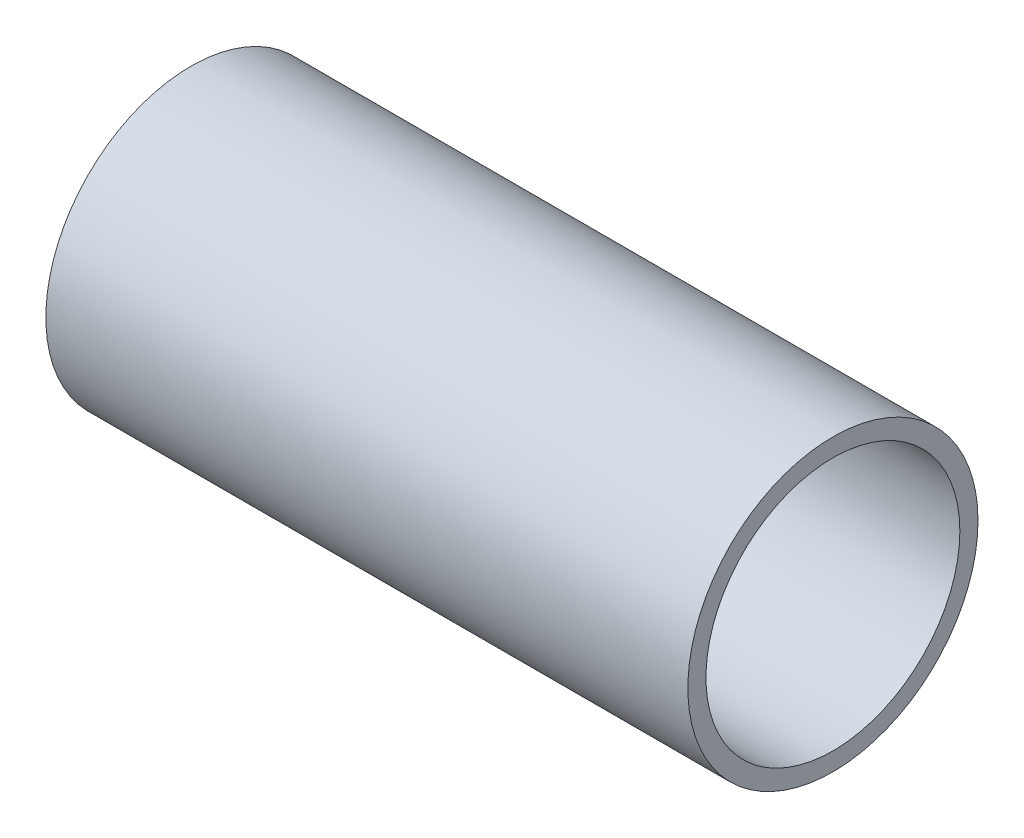
SolidWorks part; units mm, degrees
material "Bronce de aluminio"
ref_plane "Alzado" through (0, 0, 0) normal (0, 0, 1) x (1, 0, 0)
ref_plane "Planta" through (0, 0, 0) normal (0, 1, 0) x (1, 0, 0)
ref_plane "Vista lateral" through (0, 0, 0) normal (1, 0, 0) x (0, 0, -1)
sketch "Croquis1" plane through (0, 0, 0) normal (1, 0, 0) x (0, 0, -1)
  circle A0 centre (0, 0) radius 8
  circle A1 centre (0, 0) radius 7
  dimension "D1" = 14
extrude "Saliente-Extruir1" add sketch "Croquis1" along normal blind 35.4
